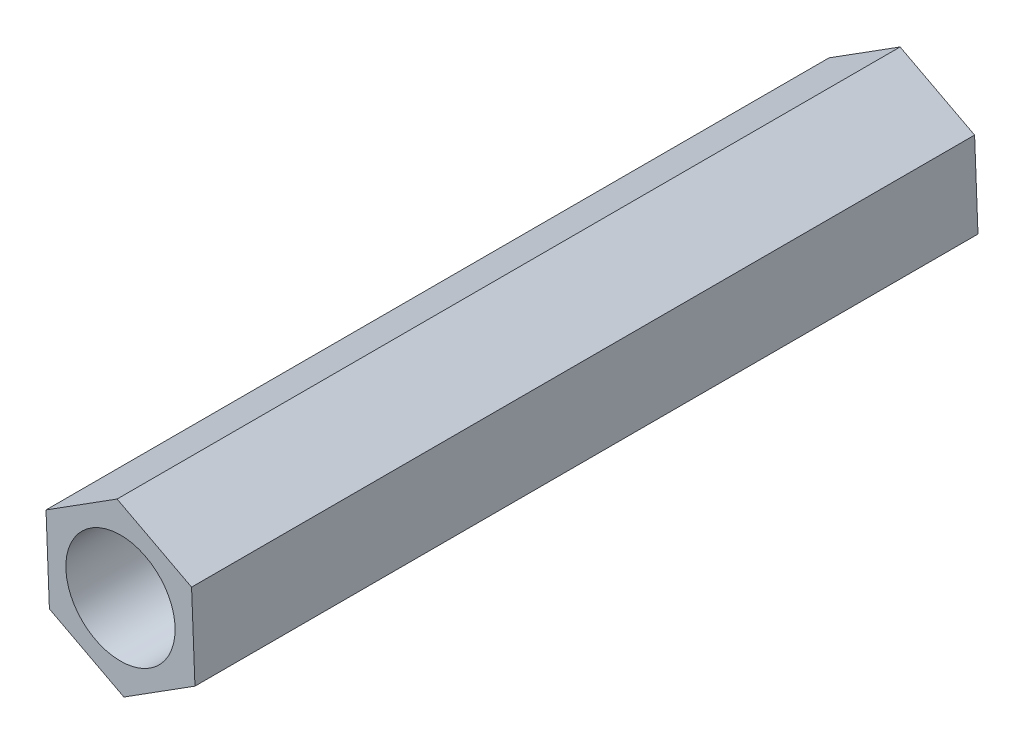
SolidWorks part; units mm, degrees
ref_plane "前视基准面" through (0, 0, 0) normal (0, 0, 1) x (1, 0, 0)
ref_plane "上视基准面" through (0, 0, 0) normal (0, 1, 0) x (1, 0, 0)
ref_plane "右视基准面" through (0, 0, 0) normal (1, 0, 0) x (0, 0, -1)
sketch "草图1" plane through (0, 0, 0) normal (0, 0, 1) x (1, 0, 0)
  line L1 (4.0903, -2.1454) -> (3.9031, 2.4696)
  line L2 (3.9031, 2.4696) -> (-0.1871, 4.615)
  line L3 (-0.1871, 4.615) -> (-4.0903, 2.1454)
  line L4 (-4.0903, 2.1454) -> (-3.9031, -2.4696)
  line L5 (-3.9031, -2.4696) -> (0.1871, -4.615)
  line L6 (0.1871, -4.615) -> (4.0903, -2.1454)
  circle A0 centre (0, 0) radius 4 construction
  dimension "D1" = 8
extrude "凸台-拉伸1" add sketch "草图1" along normal blind 43
sketch "草图2" plane through (0, 0, 43) normal (0, 0, 1) x (1, 0, 0)
  circle A0 centre (0, 0) radius 3
  dimension "D1" = 6
extrude "切除-拉伸1" cut sketch "草图2" against normal up to next
